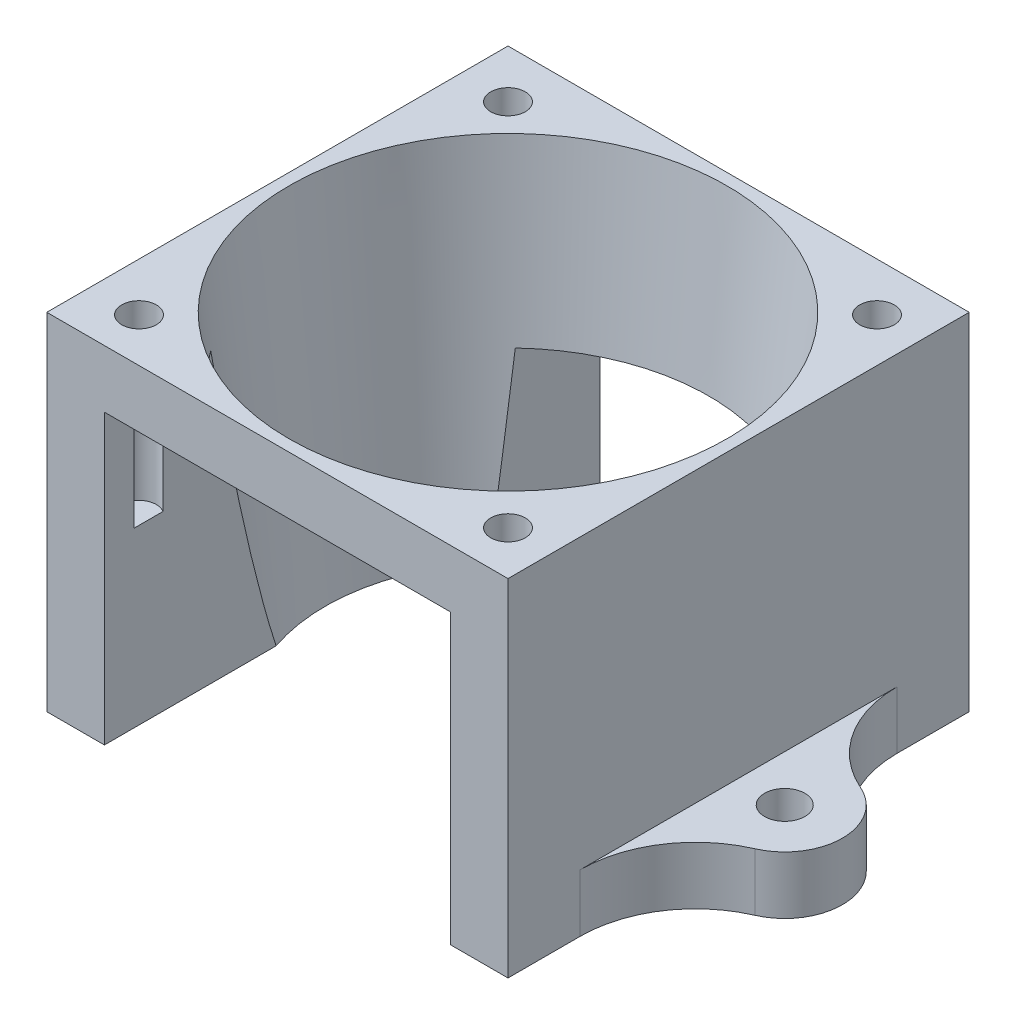
SolidWorks part; units mm, degrees
ref_plane "Front Plane" through (0, 0, 0) normal (0, 0, 1) x (1, 0, 0)
ref_plane "Top Plane" through (0, 0, 0) normal (0, 1, 0) x (1, 0, 0)
ref_plane "Right Plane" through (0, 0, 0) normal (1, 0, 0) x (0, 0, -1)
sketch "Sketch1" plane through (0, 0, 0) normal (0, 1, 0) x (1, 0, 0)
  line L1 (20, 20) -> (-20, 20)
  line L2 (20, 20) -> (20, -20)
  line L3 (20, -20) -> (-20, -20)
  line L4 (-20, 20) -> (-20, -20)
  line L5 (20, 20) -> (-20, -20) construction
  line L6 (20, -20) -> (-20, 20) construction
  point P0 (0, 0)
  dimension "D1" = 40
  dimension "D2" = 40
extrude "Boss-Extrude1" add sketch "Sketch1" along normal blind 30
sketch "Sketch2" plane through (0, 30, 0) normal (0, 1, 0) x (1, 0, 0)
  circle A0 centre (0, 0) radius 19
  dimension "D1" = 38
extrude "Cut-Extrude1" cut sketch "Sketch2" against normal blind 30 draft 6
sketch "Sketch3" plane through (0, 30, 0) normal (0, 1, 0) x (1, 0, 0)
  line L0 (0, 0) -> (-20, 20) construction
  line L1 (0, 0) -> (20, 20) construction
  line L2 (0, 0) -> (-20, -20) construction
  line L3 (0, 0) -> (20, -20) construction
  circle A0 centre (0, 0) radius 22.36 construction
  circle A1 centre (-15.8109, 15.8109) radius 1.5
  circle A2 centre (16.1891, 15.8109) radius 1.5
  circle A3 centre (16.1891, -16.1891) radius 1.5
  circle A4 centre (-15.8109, -16.1891) radius 1.5
  point P22 (0.1891, -0.1891)
  dimension "D1" = 32
  dimension "D2" = 3
  dimension "D3" = 4
extrude "Cut-Extrude2" cut sketch "Sketch3" against normal blind 15
sketch "Sketch4" plane through (0, 0, -20) normal (0, 0, -1) x (-1, 0, 0)
  line L0 (-12, 0) -> (-12, 15)
  line L1 (-12, 0) -> (12, 0)
  line L2 (-12, 15) -> (12, 15)
  line L3 (12, 0) -> (12, 15)
  line L4 (-20, 0) -> (20, 0) construction
  dimension "D1" = 15
  dimension "D2" = 24
  dimension "D3" = 12
extrude "Cut-Extrude3" cut sketch "Sketch4" against normal through all
sketch "Sketch5" plane through (0, 0, 20) normal (0, 0, 1) x (1, 0, 0)
  line L1 (-15, 0) -> (15, 0)
  line L2 (-15, 0) -> (-15, 25)
  line L3 (-15, 25) -> (15, 25)
  line L4 (15, 0) -> (15, 25)
  line L5 (-12, 15) -> (12, 15) construction
  dimension "D1" = 10
  dimension "D2" = 15
  dimension "D3" = 15
extrude "Cut-Extrude4" cut sketch "Sketch5" against normal blind 15
sketch "Sketch7" plane through (0, 0, 0) normal (0, -1, 0) x (1, 0, 0)
  line L0 (-20, 3) -> (-20, -3)
  line L1 (-20, -20) -> (-20, 20) construction
  line L2 (0, 0) -> (0, 14.9925) construction
  line L3 (20, 3) -> (20, -3)
  arc A0 (-20, 3) -> (-20, -3) centre (-24, 0) ccw
  circle A1 centre (-24, 0) radius 1.75
  circle A2 centre (24, 0) radius 1.75
  arc A3 (20, 3) -> (20, -3) centre (24, 0) cw
  dimension "D1" = 10
  dimension "D3" = 3.5
  dimension "D2" = 24
extrude "Boss-Extrude2" add sketch "Sketch7" against normal blind 5
fillet "Fillet1" radius 10 1 edges at (-20, 2.5, 3)
fillet "Fillet2" radius 10 3 edges at (20, 2.5, -3) (20, 2.5, 3) (-20, 2.5, -3)
